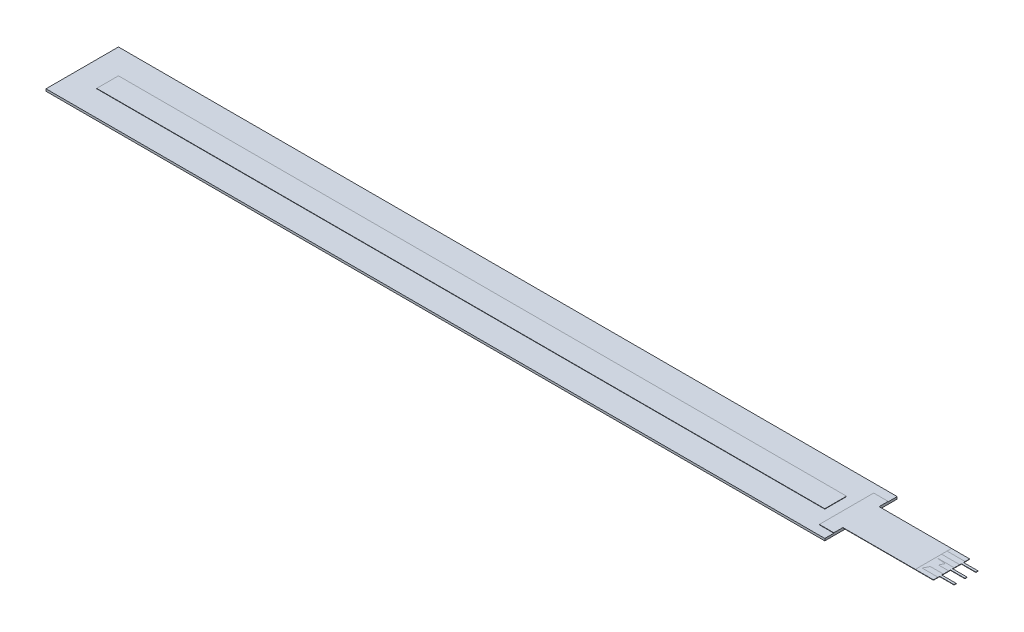
SolidWorks part; units mm, degrees
ref_plane "Front Plane" through (0, 0, 0) normal (0, 0, 1) x (1, 0, 0)
ref_plane "Top Plane" through (0, 0, 0) normal (0, 1, 0) x (1, 0, 0)
ref_plane "Right Plane" through (0, 0, 0) normal (1, 0, 0) x (0, 0, -1)
sketch "main_body" plane through (0, 0, 0) normal (0, 1, 0) x (1, 0, 0)
  line L1 (107.5, -10) -> (-107.5, -10)
  line L2 (107.5, -10) -> (107.5, 10)
  line L3 (107.5, 10) -> (-107.5, 10)
  line L4 (-107.5, -10) -> (-107.5, 10)
  line L5 (107.5, -10) -> (-107.5, 10) construction
  line L6 (107.5, 10) -> (-107.5, -10) construction
  point P0 (0, 0)
  dimension "D1" = 215
  dimension "D2" = 20
extrude "Boss-Extrude1" add sketch "main_body" along normal blind 0.6
sketch "Sketch2" plane through (0, 0.6, 0) normal (0, 1, 0) x (1, 0, 0)
  line L0 (-107.5, 10) -> (-107.5, -10) construction
  line L1 (100.5, -3) -> (-100.5, -3)
  line L2 (100.5, -3) -> (100.5, 3)
  line L3 (100.5, 3) -> (-100.5, 3)
  line L4 (-100.5, -3) -> (-100.5, 3)
  line L5 (100.5, -3) -> (-100.5, 3) construction
  line L6 (100.5, 3) -> (-100.5, -3) construction
  line L7 (107.5, 10) -> (-107.5, 10) construction
  point P0 (0, 0)
  dimension "D1" = 7
  dimension "D2" = 7
extrude "Boss-Extrude2" add sketch "Sketch2" along normal blind 0.1
sketch "Sketch3" plane through (0, 0.6, 0) normal (0, 1, 0) x (1, 0, 0)
  line L0 (107.5, -10) -> (107.5, 10) construction
  line L1 (107.5, 5) -> (127.5, 5)
  line L2 (107.5, 5) -> (107.5, -5) construction
  line L3 (107.5, -5) -> (127.5, -5)
  line L4 (127.5, 5) -> (127.5, -5)
  line L5 (103.5, -7.5) -> (103.5, 7.5)
  line L6 (0, 0) -> (127.5, 0) construction
  line L7 (103.5, 7.5) -> (107.5, 7.5)
  line L8 (107.5, 7.5) -> (107.5, 5)
  line L9 (107.5, -5) -> (107.5, -7.5)
  line L10 (107.5, -7.5) -> (103.5, -7.5)
  point P6 (127.5, 0)
  point P11 (103.5, 0)
  dimension "D1" = 20
  dimension "D2" = 10
  dimension "D3" = 15
  dimension "D4" = 4
extrude "Boss-Extrude3" add sketch "Sketch3" along normal blind 0.1
sketch "Sketch4" plane through (127.5, 0, 0) normal (1, 0, 0) x (0, 0, -1)
  line L4 (-5, 0.6) -> (5, 0.6)
  line L5 (5, 0.6) -> (5, 0.7)
  line L6 (5, 0.7) -> (-5, 0.7)
  line L7 (-5, 0.7) -> (-5, 0.6)
  line L8 (-5, 0.6) -> (5, 0.6)
  line L9 (5, 0.6) -> (5, 0.7)
  line L10 (5, 0.7) -> (-5, 0.7)
  line L11 (-5, 0.7) -> (-5, 0.6)
  dimension "D1" = 0
extrude "Boss-Extrude4" add sketch "Sketch4" along normal blind 5 separate body
sketch "Sketch5" plane through (0, 0.7, 0) normal (0, 1, 0) x (1, 0, 0)
  line L0 (127.5, -5) -> (127.5, 5) construction
  line L1 (127.5, 3.75) -> (132.5, 3.75)
  line L2 (127.5, 3.75) -> (127.5, 2.25)
  line L3 (127.5, 2.25) -> (132.5, 2.25)
  line L4 (132.5, 3.75) -> (132.5, 2.25) construction
  line L5 (132.5, 5) -> (132.5, -5) construction
  line L6 (132.5, 3.75) -> (132.5, 3.3)
  line L7 (132.5, 3.3) -> (136.5, 3.3)
  line L8 (136.5, 3.3) -> (136.5, 2.7)
  line L9 (136.5, 2.7) -> (132.5, 2.7)
  line L10 (132.5, 2.7) -> (132.5, 2.25)
  line L12 (127.5, 3) -> (136.5, 3) construction
  line L13 (82.5, 0) -> (132.5, 0) construction
  line L15 (127.5, 0.75) -> (132.5, 0.75)
  line L16 (127.5, 0.75) -> (127.5, -0.75)
  line L17 (127.5, -0.75) -> (132.5, -0.75)
  line L18 (132.5, 0.75) -> (132.5, 0.3)
  line L19 (132.5, 0.3) -> (136.5, 0.3)
  line L20 (136.5, 0.3) -> (136.5, -0.3)
  line L21 (136.5, -0.3) -> (132.5, -0.3)
  line L22 (132.5, -0.3) -> (132.5, -0.75)
  line L23 (127.5, -2.25) -> (132.5, -2.25)
  line L24 (127.5, -2.25) -> (127.5, -3.75)
  line L25 (127.5, -3.75) -> (132.5, -3.75)
  line L26 (132.5, -2.25) -> (132.5, -2.7)
  line L27 (132.5, -2.7) -> (136.5, -2.7)
  line L28 (136.5, -2.7) -> (136.5, -3.3)
  line L29 (136.5, -3.3) -> (132.5, -3.3)
  line L30 (132.5, -3.3) -> (132.5, -3.75)
  line L31 (127.5, 0) -> (136.5, 0) construction
  point P12 (132.5, 3)
  point P14 (136.5, 3)
  point P17 (126.5372, -3.75)
  point P22 (107.5, 0)
  point P39 (0, 0)
  dimension "D1" = 0.6
  dimension "D2" = 1.5
  dimension "D3" = 3
  dimension "D5" = 4
  dimension "D4" = 3
extrude "Boss-Extrude5" add sketch "Sketch5" against normal up to surface (0.1 mm away) separate body up to face at (117.5, 0.6, 0)
